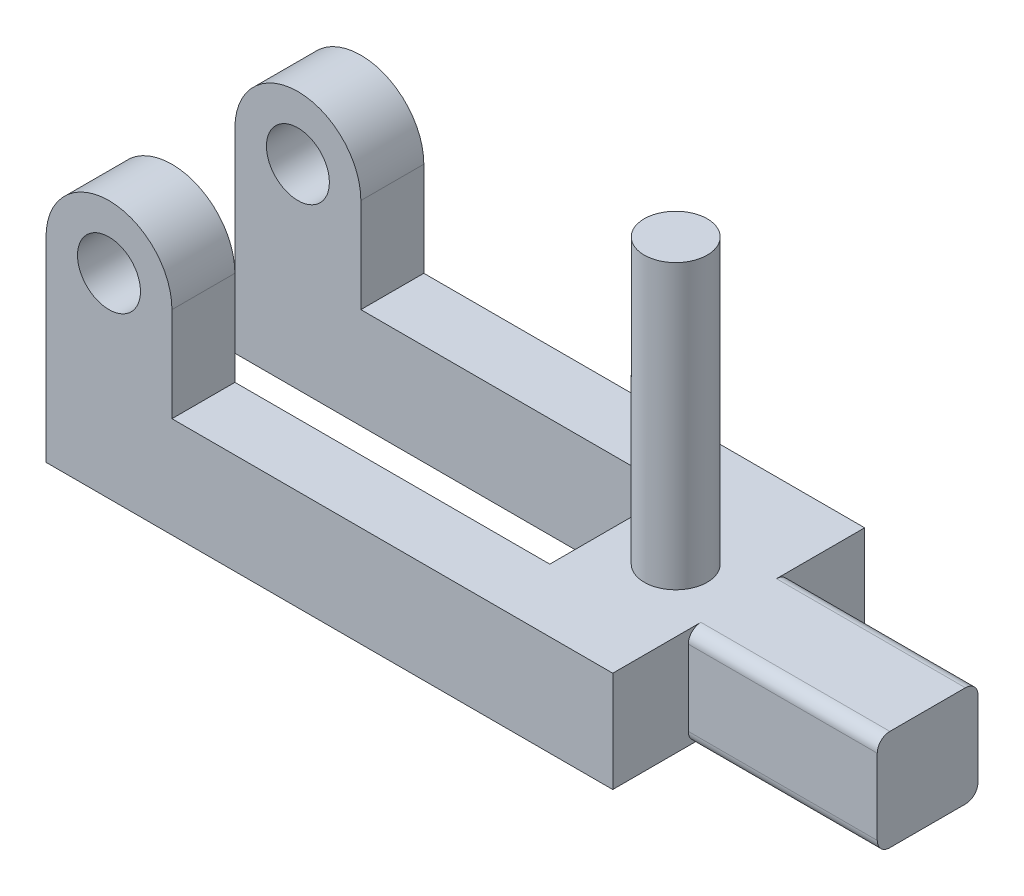
SolidWorks part; units mm, degrees
ref_plane "Front Plane" through (0, 0, 0) normal (0, 0, 1) x (1, 0, 0)
ref_plane "Top Plane" through (0, 0, 0) normal (0, 1, 0) x (1, 0, 0)
ref_plane "Right Plane" through (0, 0, 0) normal (1, 0, 0) x (0, 0, -1)
sketch "Sketch2" plane through (0, 0, 0) normal (0, 1, 0) x (1, 0, 0)
  line L0 (0, 30) -> (0, 40)
  line L1 (0, 0) -> (90, 0)
  line L2 (0, 0) -> (0, 10)
  line L3 (0, 40) -> (90, 40)
  line L4 (90, 0) -> (90, 12)
  line L5 (0, 10) -> (70, 10)
  line L7 (0, 30) -> (70, 30)
  line L8 (70, 10) -> (70, 30)
  line L9 (90, 12) -> (120, 12)
  line L11 (90, 28) -> (120, 28)
  line L12 (120, 12) -> (120, 28)
  line L13 (90, 28) -> (90, 40)
  dimension "D1" = 10
  dimension "D2" = 10
  dimension "D3" = 90
  dimension "D4" = 30
  dimension "D5" = 16
  dimension "D6" = 40
  dimension "D7" = 20
extrude "Boss-Extrude1" add sketch "Sketch2" along normal blind 16
fillet "Fillet1" radius 2 4 edges at (105, 16, -28) (105, 16, -12) (105, 0, -28) (105, 0, -12)
sketch "Sketch3" plane through (0, 0, 0) normal (0, 0, 1) x (1, 0, 0)
  line L0 (0, 0) -> (90, 0) construction
  line L1 (0, 16) -> (20, 16)
  line L2 (0, 16) -> (0, 31)
  line L3 (0, 31) -> (20, 31) construction
  line L4 (20, 16) -> (20, 31)
  arc A0 (20, 31) -> (0, 31) centre (10, 31) ccw
  circle A1 centre (10, 31) radius 5
  dimension "D1" = 20
  dimension "D2" = 31
  dimension "D3" = 10
extrude "Boss-Extrude2" add sketch "Sketch3" against normal blind 10
pattern_linear "LPattern1" count 2 spacing 30 along (0, 0, -1) of "Boss-Extrude2"
sketch "Sketch4" plane through (0, 16, 0) normal (0, 1, 0) x (1, 0, 0)
  line L0 (70, 30) -> (70, 10) construction
  circle A0 centre (80, 20) radius 5
  point P2 (0, 0)
  point P5 (70, 20)
  point P6 (83.0226, 20)
  dimension "D1" = 10
  dimension "D2" = 10
extrude "Boss-Extrude3" add sketch "Sketch4" along normal blind 45
